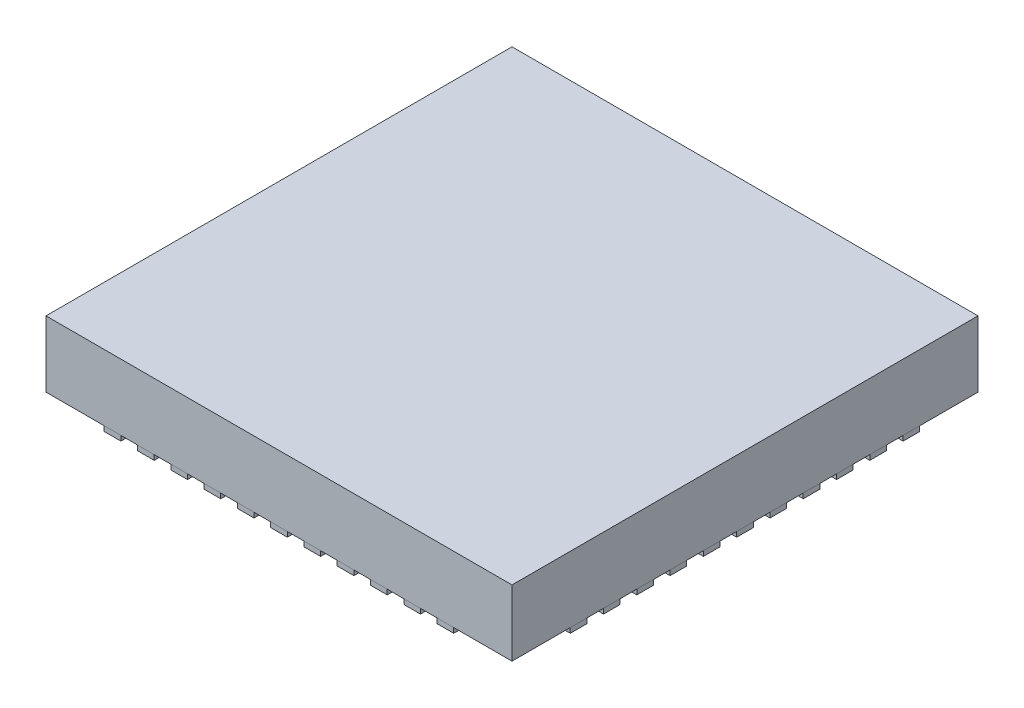
SolidWorks part; units mm, degrees
ref_plane "Front Plane" through (0, 0, 0) normal (0, 0, 1) x (1, 0, 0)
ref_plane "Top Plane" through (0, 0, 0) normal (0, 1, 0) x (1, 0, 0)
ref_plane "Right Plane" through (0, 0, 0) normal (1, 0, 0) x (0, 0, -1)
sketch "Sketch2" plane through (0, 0, 0) normal (0, 1, 0) x (1, 0, 0)
  line L1 (-3.5, 3.5) -> (3.5, 3.5)
  line L2 (-3.5, 3.5) -> (-3.5, -3.5)
  line L3 (-3.5, -3.5) -> (3.5, -3.5)
  line L4 (3.5, 3.5) -> (3.5, -3.5)
  line L5 (-3.5, 3.5) -> (3.5, -3.5) construction
  line L6 (-3.5, -3.5) -> (3.5, 3.5) construction
  point P0 (0, 0)
  dimension "D1" = 7
  dimension "D2" = 7
extrude "Boss-Extrude1" add sketch "Sketch2" along normal blind 0.9925
sketch "Sketch3" plane through (0, 0, 0) normal (0, -1, 0) x (1, 0, 0)
  line L0 (0, 3.5) -> (0, -3.5) construction
  line L1 (-3.5, 3.5) -> (3.5, 3.5) construction
  line L2 (3.5, -3.5) -> (-3.5, -3.5) construction
  line L3 (-0.625, 3.5) -> (-0.625, 2.95)
  line L4 (-3.5, 0) -> (3.5, 0) construction
  line L5 (-3.5, -3.5) -> (-3.5, 3.5) construction
  line L6 (3.5, 3.5) -> (3.5, -3.5) construction
  line L7 (-0.125, 3.5) -> (0.125, 3.5)
  line L8 (-0.125, 3.5) -> (-0.125, 2.95)
  line L9 (-0.125, 2.95) -> (0.125, 2.95)
  line L11 (-0.625, 2.95) -> (-0.375, 2.95)
  line L12 (-0.375, 3.5) -> (-0.375, 2.95)
  line L13 (-0.625, 3.5) -> (-0.375, 3.5)
  line L14 (-1.125, 3.5) -> (-1.125, 2.95)
  line L15 (-1.125, 2.95) -> (-0.875, 2.95)
  line L16 (-0.875, 3.5) -> (-0.875, 2.95)
  line L17 (-1.125, 3.5) -> (-0.875, 3.5)
  line L18 (-1.625, 3.5) -> (-1.625, 2.95)
  line L19 (-1.625, 2.95) -> (-1.375, 2.95)
  line L20 (-1.375, 3.5) -> (-1.375, 2.95)
  line L21 (-1.625, 3.5) -> (-1.375, 3.5)
  line L22 (-2.125, 3.5) -> (-2.125, 2.95)
  line L23 (-2.125, 2.95) -> (-1.875, 2.95)
  line L24 (-1.875, 3.5) -> (-1.875, 2.95)
  line L25 (-2.125, 3.5) -> (-1.875, 3.5)
  line L26 (-2.625, 3.5) -> (-2.625, 2.95)
  line L27 (-2.625, 2.95) -> (-2.375, 2.95)
  line L28 (-2.375, 3.5) -> (-2.375, 2.95)
  line L29 (-2.625, 3.5) -> (-2.375, 3.5)
  line L30 (-3.5, -0.625) -> (-2.95, -0.625)
  line L31 (-2.95, 0.125) -> (-2.95, -0.125)
  line L32 (-3.5, 3.5) -> (0, 0) construction
  line L33 (-3.5, -0.125) -> (-2.95, -0.125)
  line L34 (-3.5, 2.625) -> (-3.5, 2.375)
  line L35 (-3.5, 2.375) -> (-2.95, 2.375)
  line L36 (-2.95, 2.625) -> (-2.95, 2.375)
  line L37 (-3.5, 2.625) -> (-2.95, 2.625)
  line L38 (-3.5, 2.125) -> (-3.5, 1.875)
  line L39 (-3.5, 1.875) -> (-2.95, 1.875)
  line L40 (-2.95, 2.125) -> (-2.95, 1.875)
  line L41 (-3.5, 2.125) -> (-2.95, 2.125)
  line L42 (-3.5, 1.625) -> (-3.5, 1.375)
  line L43 (-3.5, 1.375) -> (-2.95, 1.375)
  line L44 (-2.95, 1.625) -> (-2.95, 1.375)
  line L45 (-3.5, 1.625) -> (-2.95, 1.625)
  line L46 (-3.5, 1.125) -> (-3.5, 0.875)
  line L47 (-3.5, 0.875) -> (-2.95, 0.875)
  line L48 (-2.95, 1.125) -> (-2.95, 0.875)
  line L49 (-3.5, 1.125) -> (-2.95, 1.125)
  line L50 (-3.5, 0.625) -> (-3.5, 0.375)
  line L51 (-3.5, 0.375) -> (-2.95, 0.375)
  line L52 (-2.95, 0.625) -> (-2.95, 0.375)
  line L53 (-3.5, 0.125) -> (-2.95, 0.125)
  line L54 (-3.5, 0.625) -> (-2.95, 0.625)
  line L55 (-2.95, -0.625) -> (-2.95, -0.375)
  line L56 (2.625, 3.5) -> (2.375, 3.5)
  line L57 (2.375, 3.5) -> (2.375, 2.95)
  line L58 (2.625, 2.95) -> (2.375, 2.95)
  line L59 (2.625, 3.5) -> (2.625, 2.95)
  line L60 (2.125, 3.5) -> (1.875, 3.5)
  line L61 (1.875, 3.5) -> (1.875, 2.95)
  line L62 (2.125, 2.95) -> (1.875, 2.95)
  line L63 (2.125, 3.5) -> (2.125, 2.95)
  line L64 (1.625, 3.5) -> (1.375, 3.5)
  line L65 (1.375, 3.5) -> (1.375, 2.95)
  line L66 (1.625, 2.95) -> (1.375, 2.95)
  line L67 (1.625, 3.5) -> (1.625, 2.95)
  line L68 (1.125, 3.5) -> (0.875, 3.5)
  line L69 (0.875, 3.5) -> (0.875, 2.95)
  line L70 (1.125, 2.95) -> (0.875, 2.95)
  line L71 (1.125, 3.5) -> (1.125, 2.95)
  line L72 (0.625, 3.5) -> (0.375, 3.5)
  line L73 (-3.5, -3.5) -> (0, 0) construction
  line L75 (0.375, 3.5) -> (0.375, 2.95)
  line L76 (0.625, 2.95) -> (0.375, 2.95)
  line L77 (0.125, 3.5) -> (0.125, 2.95)
  line L78 (0.625, 3.5) -> (0.625, 2.95)
  line L79 (-3.5, -0.375) -> (-2.95, -0.375)
  line L80 (-3.5, -0.625) -> (-3.5, -0.375)
  line L81 (-3.5, -1.125) -> (-2.95, -1.125)
  line L82 (-2.95, -1.125) -> (-2.95, -0.875)
  line L83 (-3.5, -0.875) -> (-2.95, -0.875)
  line L84 (-3.5, -1.125) -> (-3.5, -0.875)
  line L85 (-3.5, -1.625) -> (-2.95, -1.625)
  line L86 (-2.95, -1.625) -> (-2.95, -1.375)
  line L87 (-3.5, -1.375) -> (-2.95, -1.375)
  line L88 (-3.5, -1.625) -> (-3.5, -1.375)
  line L89 (-3.5, -2.125) -> (-2.95, -2.125)
  line L90 (-2.95, -2.125) -> (-2.95, -1.875)
  line L91 (-3.5, -1.875) -> (-2.95, -1.875)
  line L92 (-3.5, -2.125) -> (-3.5, -1.875)
  line L93 (-3.5, -2.625) -> (-2.95, -2.625)
  line L94 (-2.95, -2.625) -> (-2.95, -2.375)
  line L95 (-3.5, -2.375) -> (-2.95, -2.375)
  line L96 (-3.5, -2.625) -> (-3.5, -2.375)
  line L97 (-3.5, -0.125) -> (-3.5, 0.125)
  line L98 (3.5, -0.125) -> (3.5, 0.125)
  line L99 (3.5, -2.625) -> (3.5, -2.375)
  line L100 (3.5, -2.375) -> (2.95, -2.375)
  line L101 (2.95, -2.625) -> (2.95, -2.375)
  line L102 (3.5, -2.625) -> (2.95, -2.625)
  line L103 (3.5, -2.125) -> (3.5, -1.875)
  line L104 (3.5, -1.875) -> (2.95, -1.875)
  line L105 (2.95, -2.125) -> (2.95, -1.875)
  line L106 (3.5, -2.125) -> (2.95, -2.125)
  line L107 (3.5, -1.625) -> (3.5, -1.375)
  line L108 (3.5, -1.375) -> (2.95, -1.375)
  line L109 (2.95, -1.625) -> (2.95, -1.375)
  line L110 (3.5, -1.625) -> (2.95, -1.625)
  line L111 (3.5, -1.125) -> (3.5, -0.875)
  line L112 (3.5, -0.875) -> (2.95, -0.875)
  line L113 (2.95, -1.125) -> (2.95, -0.875)
  line L114 (3.5, -1.125) -> (2.95, -1.125)
  line L115 (3.5, -0.625) -> (3.5, -0.375)
  line L116 (3.5, -0.375) -> (2.95, -0.375)
  line L117 (2.95, -0.625) -> (2.95, -0.375)
  line L118 (3.5, 0.625) -> (2.95, 0.625)
  line L119 (3.5, 0.125) -> (2.95, 0.125)
  line L120 (2.95, 0.625) -> (2.95, 0.375)
  line L121 (3.5, 0.375) -> (2.95, 0.375)
  line L122 (3.5, 0.625) -> (3.5, 0.375)
  line L123 (3.5, 1.125) -> (2.95, 1.125)
  line L124 (2.95, 1.125) -> (2.95, 0.875)
  line L125 (3.5, 0.875) -> (2.95, 0.875)
  line L126 (3.5, 1.125) -> (3.5, 0.875)
  line L127 (3.5, 1.625) -> (2.95, 1.625)
  line L128 (2.95, 1.625) -> (2.95, 1.375)
  line L129 (3.5, 1.375) -> (2.95, 1.375)
  line L130 (3.5, 1.625) -> (3.5, 1.375)
  line L131 (3.5, 2.125) -> (2.95, 2.125)
  line L132 (2.95, 2.125) -> (2.95, 1.875)
  line L133 (3.5, 1.875) -> (2.95, 1.875)
  line L134 (3.5, 2.125) -> (3.5, 1.875)
  line L135 (3.5, 2.625) -> (2.95, 2.625)
  line L136 (2.95, 2.625) -> (2.95, 2.375)
  line L137 (3.5, 2.375) -> (2.95, 2.375)
  line L138 (3.5, 2.625) -> (3.5, 2.375)
  line L139 (3.5, -0.125) -> (2.95, -0.125)
  line L140 (2.95, 0.125) -> (2.95, -0.125)
  line L141 (3.5, -0.625) -> (2.95, -0.625)
  line L142 (-0.125, -3.5) -> (0.125, -3.5)
  line L143 (-0.125, -3.5) -> (-0.125, -2.95)
  line L144 (0.125, -3.5) -> (0.125, -2.95)
  line L145 (-0.125, -2.95) -> (0.125, -2.95)
  line L146 (0.625, -3.5) -> (0.625, -2.95)
  line L147 (0.625, -2.95) -> (0.375, -2.95)
  line L148 (0.375, -3.5) -> (0.375, -2.95)
  line L149 (0.625, -3.5) -> (0.375, -3.5)
  line L150 (1.125, -3.5) -> (1.125, -2.95)
  line L151 (1.125, -2.95) -> (0.875, -2.95)
  line L152 (0.875, -3.5) -> (0.875, -2.95)
  line L153 (1.125, -3.5) -> (0.875, -3.5)
  line L154 (1.625, -3.5) -> (1.625, -2.95)
  line L155 (1.625, -2.95) -> (1.375, -2.95)
  line L156 (1.375, -3.5) -> (1.375, -2.95)
  line L157 (1.625, -3.5) -> (1.375, -3.5)
  line L158 (2.125, -3.5) -> (2.125, -2.95)
  line L159 (2.125, -2.95) -> (1.875, -2.95)
  line L160 (1.875, -3.5) -> (1.875, -2.95)
  line L161 (2.125, -3.5) -> (1.875, -3.5)
  line L162 (2.625, -3.5) -> (2.625, -2.95)
  line L163 (2.625, -2.95) -> (2.375, -2.95)
  line L164 (2.375, -3.5) -> (2.375, -2.95)
  line L165 (2.625, -3.5) -> (2.375, -3.5)
  line L166 (-2.625, -3.5) -> (-2.375, -3.5)
  line L167 (-2.375, -3.5) -> (-2.375, -2.95)
  line L168 (-2.625, -2.95) -> (-2.375, -2.95)
  line L169 (-2.625, -3.5) -> (-2.625, -2.95)
  line L170 (-2.125, -3.5) -> (-1.875, -3.5)
  line L171 (-1.875, -3.5) -> (-1.875, -2.95)
  line L172 (-2.125, -2.95) -> (-1.875, -2.95)
  line L173 (-2.125, -3.5) -> (-2.125, -2.95)
  line L174 (-1.625, -3.5) -> (-1.375, -3.5)
  line L175 (-1.375, -3.5) -> (-1.375, -2.95)
  line L176 (-1.625, -2.95) -> (-1.375, -2.95)
  line L177 (-1.625, -3.5) -> (-1.625, -2.95)
  line L178 (-1.125, -3.5) -> (-0.875, -3.5)
  line L179 (-0.875, -3.5) -> (-0.875, -2.95)
  line L180 (-1.125, -2.95) -> (-0.875, -2.95)
  line L181 (-1.125, -3.5) -> (-1.125, -2.95)
  line L182 (-0.625, -3.5) -> (-0.375, -3.5)
  line L183 (-0.375, -3.5) -> (-0.375, -2.95)
  line L184 (-0.625, -2.95) -> (-0.375, -2.95)
  line L185 (-0.625, -3.5) -> (-0.625, -2.95)
  point P16 (0, 3.5)
  dimension "D1" = 0.25
  dimension "D2" = 0.55
  dimension "D4" = 6
extrude "Boss-Extrude2" add sketch "Sketch3" along normal blind 0.075 separate body
